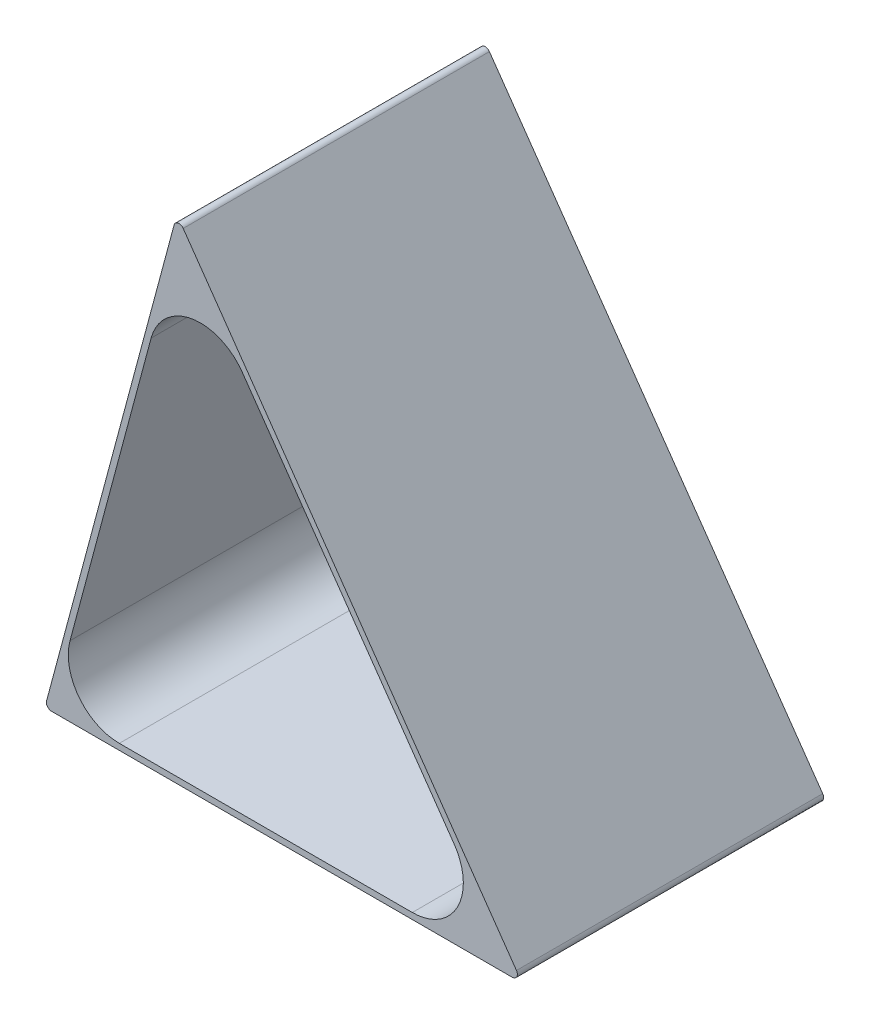
SolidWorks part; units mm, degrees
ref_plane "Plan de face" through (0, 0, 0) normal (0, 0, 1) x (1, 0, 0)
ref_plane "Plan de dessus" through (0, 0, 0) normal (0, 1, 0) x (1, 0, 0)
ref_plane "Plan de droite" through (0, 0, 0) normal (1, 0, 0) x (0, 0, -1)
sketch "Esquisse1" plane through (0, 0, 0) normal (0, 0, 1) x (1, 0, 0)
  line L0 (-46.7584, 0) -> (46.7584, 0)
  line L1 (-46.7584, 0) -> (-20.8765, 96.5926)
  line L2 (-20.8765, 96.5926) -> (46.7584, 0)
  line L3 (-45.1945, 1.2) -> (-20.3834, 93.7963)
  line L4 (-20.3834, 93.7963) -> (44.4532, 1.2)
  line L5 (-45.1945, 1.2) -> (44.4532, 1.2)
  point P0 (-47.7758, 0)
  point P4 (0, 0)
  dimension "D1" = 75
  dimension "D2" = 100
  dimension "D3" = 55
  dimension "D4" = 1.2
extrude "Boss.-Extru.1" add sketch "Esquisse1" along normal blind 60
fillet "Congé1" radius 10 3 edges at (44.4532, 1.2, 30) (-45.1945, 1.2, 30) (-20.3834, 93.7963, 30)
sketch "Esquisse2" plane through (0, 0, 0) normal (0, -1, 0) x (1, 0, 0)
  text T0 "75" font "Century Gothic" height in points 36
  text T1 "55\r\n" font "Century Gothic" height in points 36
extrude "Enlèv. mat.-Extru.1" cut sketch "Esquisse2" against normal blind 0.4
sketch "Esquisse3" plane through (-43.6262, 11.6896, 0) normal (-0.9659, 0.2588, 0) x (0, 0, 1)
  text T0 "50" font "Century Gothic" height in points 36
extrude "Enlèv. mat.-Extru.2" cut sketch "Esquisse3" against normal blind 0.4
fillet "Congé2" radius 1 3 edges at (46.7584, 0, 30) (-46.7584, 0, 30) (-20.8765, 96.5926, 30)
